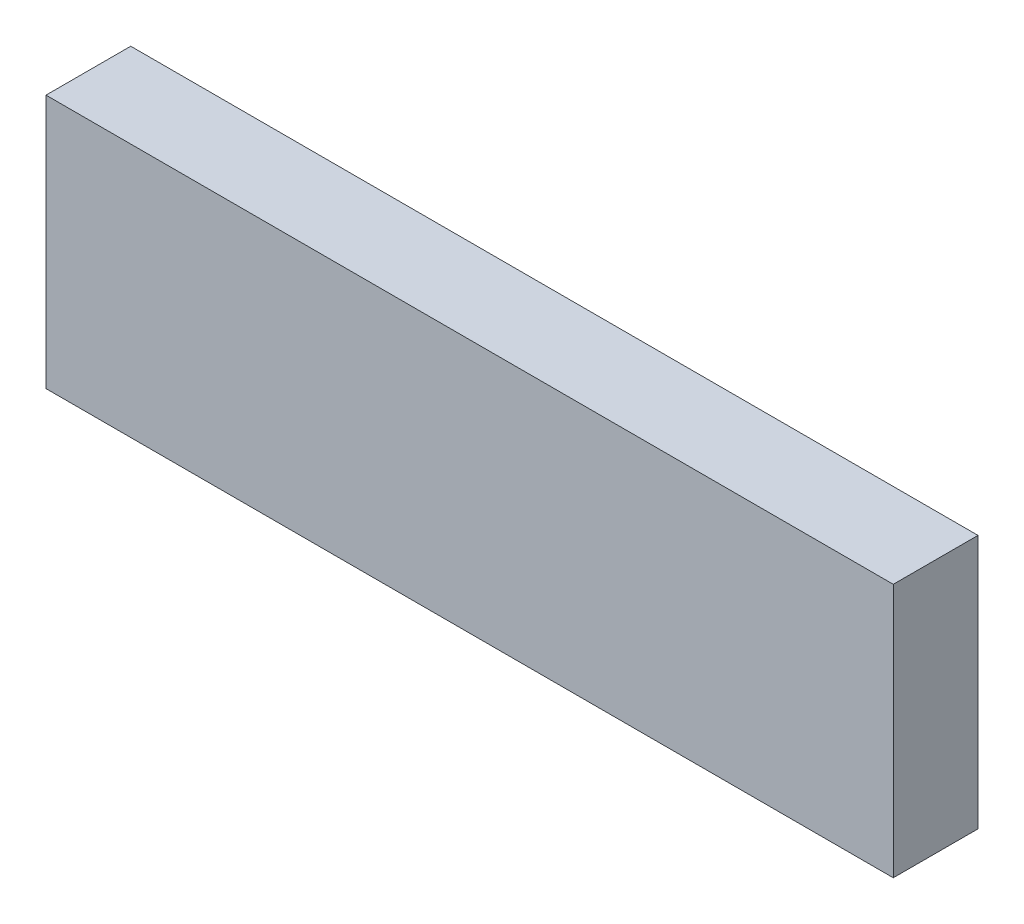
SolidWorks part; units mm, degrees
ref_plane "Front Plane" through (0, 0, 0) normal (0, 0, 1) x (1, 0, 0)
ref_plane "Top Plane" through (0, 0, 0) normal (0, 1, 0) x (1, 0, 0)
ref_plane "Right Plane" through (0, 0, 0) normal (1, 0, 0) x (0, 0, -1)
sketch "Sketch1" plane through (0, 0, 0) normal (0, 0, 1) x (1, 0, 0)
  line L1 (-17.907, 9.4774) -> (45.593, 9.4774)
  line L2 (-17.907, 9.4774) -> (-17.907, -9.5726)
  line L3 (-17.907, -9.5726) -> (45.593, -9.5726)
  line L4 (45.593, 9.4774) -> (45.593, -9.5726)
  dimension "D1" = 19.05
  dimension "D2" = 63.5
extrude "Boss-Extrude1" add sketch "Sketch1" along normal blind 6.35
